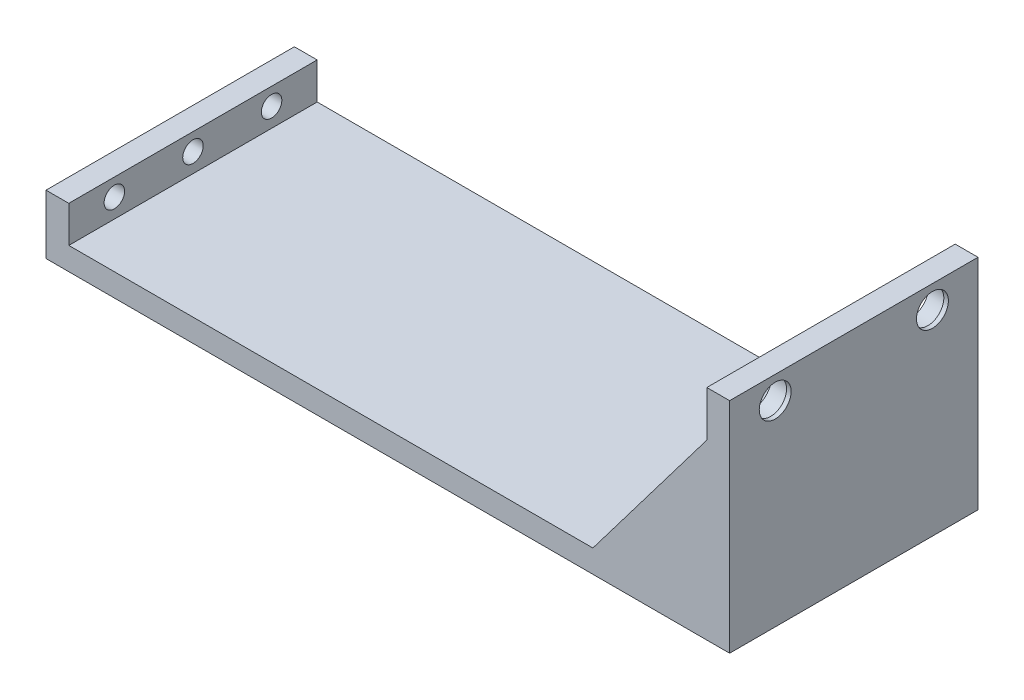
SolidWorks part; units mm, degrees
ref_plane "Front Plane" through (0, 0, 0) normal (0, 0, 1) x (1, 0, 0)
ref_plane "Top Plane" through (0, 0, 0) normal (0, 1, 0) x (1, 0, 0)
ref_plane "Right Plane" through (0, 0, 0) normal (1, 0, 0) x (0, 0, -1)
sketch "Sketch1" plane through (0, 0, 0) normal (0, 1, 0) x (1, 0, 0)
  line L2 (56.8875, -28.9394) -> (-93.1125, -28.9394)
  line L3 (56.8875, -28.9394) -> (56.8875, 25.5606)
  line L4 (56.8875, 25.5606) -> (-93.1125, 25.5606)
  line L5 (-93.1125, -28.9394) -> (-93.1125, 25.5606)
  dimension "D1" = 150
  dimension "D2" = 54.5
extrude "Boss-Extrude1" add sketch "Sketch1" along normal blind 5
sketch "Sketch2" plane through (0, 5, 0) normal (0, 1, 0) x (1, 0, 0)
  line L0 (-93.1125, -28.9394) -> (56.8875, -28.9394) construction
  line L1 (-93.1125, 25.5606) -> (-88.1125, 25.5606)
  line L2 (-93.1125, 25.5606) -> (-93.1125, -28.9394)
  line L3 (-93.1125, -28.9394) -> (-88.1125, -28.9394)
  line L4 (-88.1125, 25.5606) -> (-88.1125, -28.9394)
  dimension "D1" = 5
extrude "Boss-Extrude2" add sketch "Sketch2" along normal blind 8
hole_wizard "#8 Clearance Hole1" positions "3DSketch1" profile "Sketch3" hole size "#8" standard "ANSI Inch"
sketch3d "3DSketch1"
  line L1 (-93.1125, 13, -25.5606) -> (-93.1125, 13, 28.9394) construction
  line L2 (-93.1125, 13, -25.5606) -> (-93.1125, 0, -25.5606) construction
  line L3 (-93.1125, 13, 28.9394) -> (-93.1125, 0, 28.9394) construction
  point P0 (-93.1125, 9.2, -15.5606)
  point P2 (-93.1125, 9.2, 1.6894)
  point P4 (-93.1125, 9.2, 18.9394)
  dimension "D1" = 3.8
  dimension "D2" = 3.8
  dimension "D3" = 3.8
  dimension "D4" = 10
  dimension "D5" = 27.25
  dimension "D6" = 10
sketch "Sketch3" plane through (-93.1125, 9.2, -15.5606) normal (0, 1, 0) x (0, 0, 1)
  line L0 (0, 0) -> (0, 18.3507)
  line L1 (0, 18.3507) -> (2.2479, 17)
  line L2 (2.2479, 17) -> (2.2479, 0)
  line L5 (2.2479, 0) -> (0, 0)
  line L10 (0, 18.3507) -> (-2.2479, 17) construction
  line L11 (0, -6.35) -> (0, 107.95) construction
  dimension "Hole Dia." = 4.4958
  dimension "Hole Depth" = 17
  dimension "Drill Angle" = 118
sketch "Sketch7" plane through (0, 5, 0) normal (0, 1, 0) x (1, 0, 0)
  line L0 (56.8875, 25.5606) -> (-88.1125, 25.5606) construction
  line L1 (56.8875, -28.9394) -> (51.8875, -28.9394)
  line L2 (56.8875, -28.9394) -> (56.8875, 25.5606)
  line L3 (56.8875, 25.5606) -> (51.8875, 25.5606)
  line L4 (51.8875, -28.9394) -> (51.8875, 25.5606)
  dimension "D1" = 5
extrude "Boss-Extrude3" add sketch "Sketch7" along normal blind 43
sketch "Sketch8" plane through (51.8875, 0, 0) normal (-1, 0, 0) x (0, 0, 1)
  line L0 (-25.5606, 48) -> (28.9394, 48) construction
  line L1 (-25.5606, 48) -> (-25.5606, 5) construction
  line L2 (28.9394, 48) -> (28.9394, 5) construction
  circle A0 centre (-15.5606, 43) radius 4.25
  circle A1 centre (18.9394, 43) radius 4.25
  dimension "D1" = 8.5
  dimension "D2" = 8.5
  dimension "D3" = 5
  dimension "D4" = 5
  dimension "D5" = 10
  dimension "D6" = 10
extrude "Cut-Extrude1" cut sketch "Sketch8" against normal blind 4
sketch "Sketch10" plane through (0, 0, -25.5606) normal (0, 0, -1) x (-1, 0, 0)
  line L0 (-51.8875, 38) -> (-26.8875, 5)
  line L1 (-51.8875, 48) -> (-51.8875, 5) construction
  line L2 (-51.8875, 5) -> (88.1125, 5) construction
  dimension "D1" = 10
  dimension "D2" = 25
rib "Rib1" sketch "Sketch10" sketch "Sketch10" thickness 10 extrusion direction parallel to sketch draft on no parameters "D1"=10
sketch "Sketch12" plane through (0, 0, 28.9394) normal (0, 0, 1) x (1, 0, 0)
  line L0 (51.8875, 38) -> (26.8875, 5)
  line L1 (51.8875, 48) -> (51.8875, 5) construction
  line L2 (-88.1125, 5) -> (51.8875, 5) construction
  dimension "D1" = 10
  dimension "D2" = 25
rib "Rib3" sketch "Sketch12" sketch "Sketch12" thickness 10 extrusion direction parallel to sketch draft on no parameters "D1"=10
sketch "Sketch13" plane through (51.8875, 0, 0) normal (-1, 0, 0) x (0, 0, 1)
  line L0 (-25.5606, 48) -> (28.9394, 48) construction
  line L1 (-2.3106, 38) -> (5.6894, 38)
  line L2 (-2.3106, 38) -> (-2.3106, 36)
  line L3 (-2.3106, 36) -> (5.6894, 36)
  line L4 (5.6894, 38) -> (5.6894, 36)
  line L5 (-25.5606, 48) -> (-25.5606, 38) construction
  line L6 (28.9394, 48) -> (28.9394, 38) construction
  dimension "D1" = 8
  dimension "D2" = 10
  dimension "D3" = 23.25
  dimension "D4" = 23.25
  dimension "D5" = 2
extrude "Boss-Extrude4" add sketch "Sketch13" along normal blind 5
sketch "Sketch14" plane through (0, 38, 0) normal (0, 1, 0) x (1, 0, 0)
  line L0 (46.8875, -5.6894) -> (46.8875, 2.3106) construction
  line L1 (46.8875, 2.3106) -> (51.8875, 2.3106) construction
  circle A0 centre (49.3875, -1.6894) radius 2
  dimension "D1" = 2.5
  dimension "D2" = 4
extrude "Cut-Extrude2" cut sketch "Sketch14" against normal blind 2
sketch "Sketch15" plane through (55.8875, 0, 0) normal (-1, 0, 0) x (0, 0, 1)
  line L0 (28.9394, 48) -> (-25.5606, 48) construction
  circle A0 centre (-15.5606, 43) radius 3.5
  circle A1 centre (18.9394, 43) radius 3.5
  dimension "D1" = 5
  dimension "D2" = 5
extrude "Cut-Extrude3" cut sketch "Sketch15" against normal blind 1
